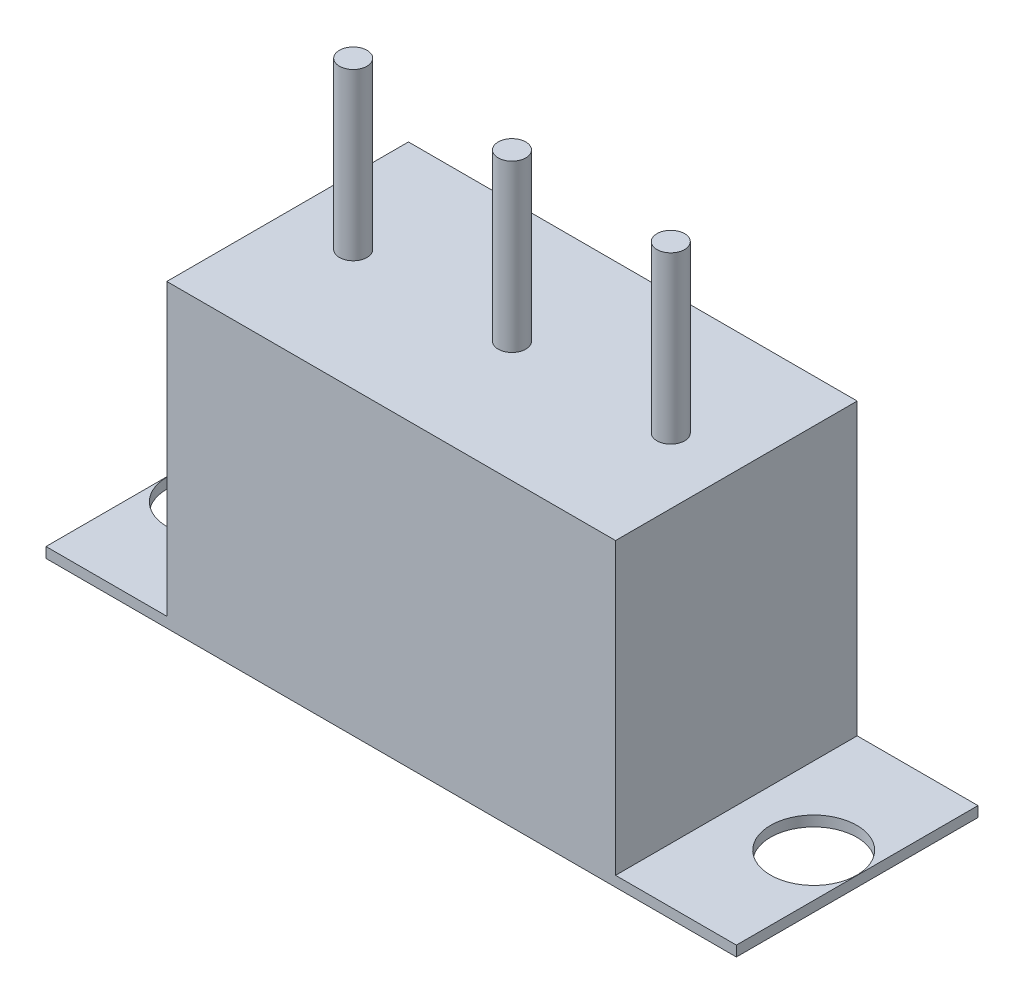
SolidWorks part; units mm, degrees
ref_plane "Front Plane" through (0, 0, 0) normal (0, 0, 1) x (1, 0, 0)
ref_plane "Top Plane" through (0, 0, 0) normal (0, 1, 0) x (1, 0, 0)
ref_plane "Right Plane" through (0, 0, 0) normal (1, 0, 0) x (0, 0, -1)
sketch "Sketch1" plane through (0, 0, 0) normal (0, 1, 0) x (1, 0, 0)
  line L1 (10, -3.5) -> (-10, -3.5)
  line L2 (10, -3.5) -> (10, 3.5)
  line L3 (10, 3.5) -> (-10, 3.5)
  line L4 (-10, -3.5) -> (-10, 3.5)
  line L5 (10, -3.5) -> (-10, 3.5) construction
  line L6 (10, 3.5) -> (-10, -3.5) construction
  point P0 (0, 0)
  dimension "D1" = 20
  dimension "D2" = 7
extrude "Boss-Extrude1" add sketch "Sketch1" along normal blind 0.3
sketch "Sketch2" plane through (0, 0.3, 0) normal (0, 1, 0) x (1, 0, 0)
  line L1 (6.5, -3.5) -> (-6.5, -3.5)
  line L2 (6.5, -3.5) -> (6.5, 3.5)
  line L3 (6.5, 3.5) -> (-6.5, 3.5)
  line L4 (-6.5, -3.5) -> (-6.5, 3.5)
  line L5 (6.5, -3.5) -> (-6.5, 3.5) construction
  line L6 (6.5, 3.5) -> (-6.5, -3.5) construction
  point P0 (0, 0)
  dimension "D1" = 7
  dimension "D2" = 13
extrude "Boss-Extrude2" add sketch "Sketch2" along normal blind 8.4
sketch "Sketch3" plane through (0, 0.3, 0) normal (0, 1, 0) x (1, 0, 0)
  line L0 (-10, 3.5) -> (-10, -3.5) construction
  circle A0 centre (-8.74, 0) radius 1.25
  circle A1 centre (8.74, 0) radius 1.25
  point P2 (-10, 0)
  dimension "D1" = 1.26
  dimension "D2" = 17.48
extrude "Cut-Extrude5" cut sketch "Sketch3" against normal up to next
sketch "Sketch4" plane through (0, 8.7, 0) normal (0, 1, 0) x (1, 0, 0)
  circle A0 centre (-4.6, 0) radius 0.4
  circle A1 centre (0, 0) radius 0.4
  circle A2 centre (4.6, 0) radius 0.4
  dimension "D1" = 4.6
  dimension "D2" = 4.6
extrude "Boss-Extrude3" add sketch "Sketch4" along normal blind 4.8
